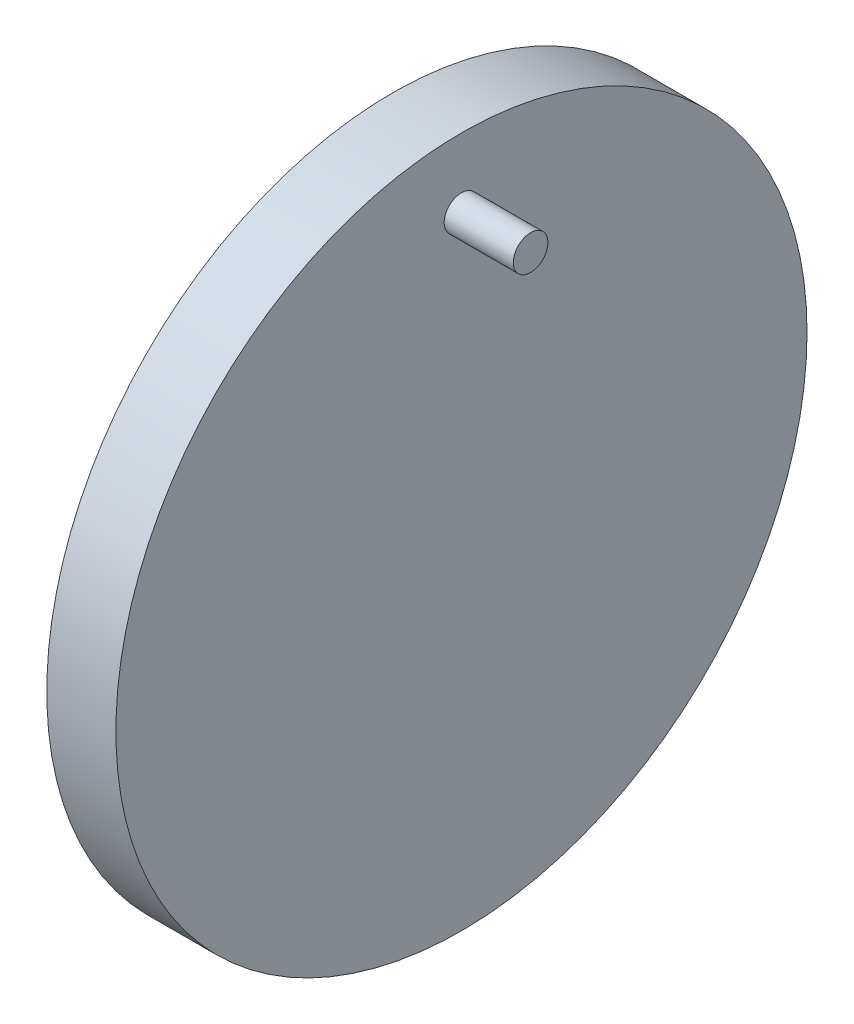
SolidWorks part; units mm, degrees
ref_plane "Front Plane" through (0, 0, 0) normal (0, 0, 1) x (1, 0, 0)
ref_plane "Top Plane" through (0, 0, 0) normal (0, 1, 0) x (1, 0, 0)
ref_plane "Right Plane" through (0, 0, 0) normal (1, 0, 0) x (0, 0, -1)
sketch "Sketch1" plane through (0, 0, 0) normal (1, 0, 0) x (0, 0, -1)
  circle A0 centre (0, 0) radius 50
  dimension "D1" = 100
extrude "Boss-Extrude1" add sketch "Sketch1" along normal blind 10
sketch "Sketch2" plane through (10, 0, 0) normal (1, 0, 0) x (0, 0, -1)
  circle A0 centre (0, 40) radius 2.5
  dimension "D1" = 5
  dimension "D2" = 40
extrude "Boss-Extrude2" add sketch "Sketch2" along normal blind 10
